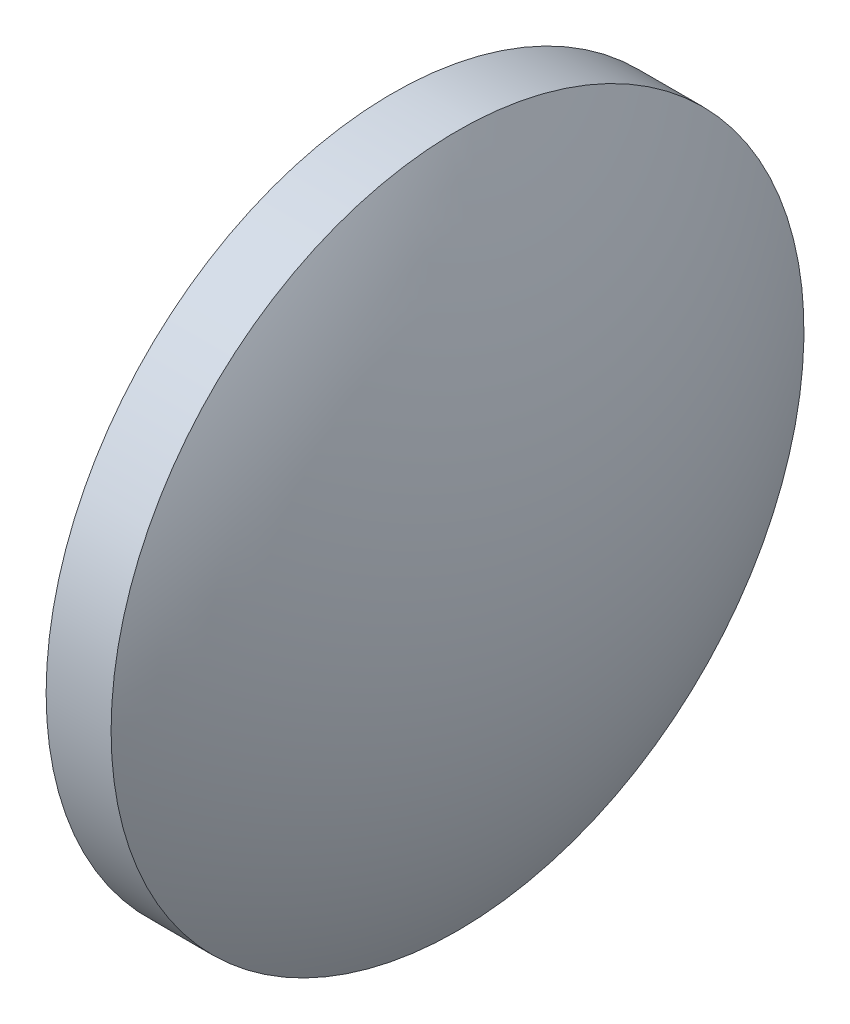
SolidWorks part; units mm, degrees
ref_plane "前视基准面" through (0, 0, 0) normal (0, 0, 1) x (1, 0, 0)
ref_plane "上视基准面" through (0, 0, 0) normal (0, 1, 0) x (1, 0, 0)
ref_plane "右视基准面" through (0, 0, 0) normal (1, 0, 0) x (0, 0, -1)
sketch "草图1" plane through (0, 0, 0) normal (0, 0, 1) x (1, 0, 0)
  line L0 (391.3668, 34.8639) -> (399.6342, 34.8639) construction
  line L1 (393.2897, 34.8639) -> (393.2897, 42.8639)
  line L2 (396.8897, 34.8639) -> (393.2897, 34.8639)
  line L5 (393.2897, 42.8639) -> (394.7897, 42.8639)
  arc A0 (396.8897, 34.8639) -> (394.7897, 42.8639) centre (380.6016, 34.8639) ccw
revolve "旋转1" add sketch "草图1" angle 360 about L0
